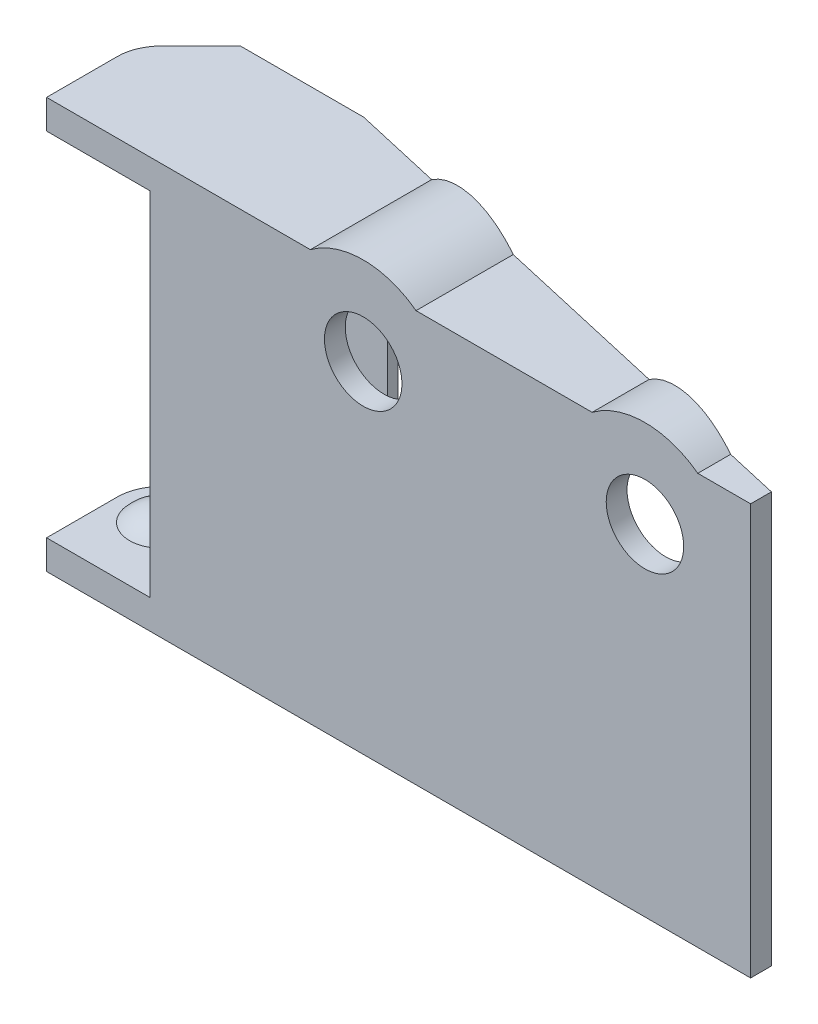
SolidWorks part; units mm, degrees
ref_plane "Front Plane" through (0, 0, 0) normal (0, 0, 1) x (1, 0, 0)
ref_plane "Top Plane" through (0, 0, 0) normal (0, 1, 0) x (1, 0, 0)
ref_plane "Right Plane" through (0, 0, 0) normal (1, 0, 0) x (0, 0, -1)
sketch "Sketch1" plane through (0, 0, 0) normal (0, 0, 1) x (1, 0, 0)
  line L0 (-6.35, 0) -> (6.35, 0)
  line L1 (6.35, 0) -> (6.35, -9.525)
  line L2 (6.35, -9.525) -> (-6.35, -9.525)
  line L3 (-6.35, -9.525) -> (-6.35, 0)
  point P3 (0, -9.525)
  point P6 (0, 0)
  dimension "D1" = 9.525
  dimension "D2" = 12.7
sketch "Sketch3" plane through (0, 0, 0) normal (0, 1, 0) x (1, 0, 0)
  line L0 (6.35, 0) -> (-6.35, 0) construction
  line L1 (-6.35, 0) -> (6.35, 0) construction
  circle A0 centre (-6.35, 3.175) radius 3.175
  circle A1 centre (6.35, 3.175) radius 3.175
  dimension "D1" = 6.35
sketch "Sketch6" plane through (0, 0, 0) normal (0, 1, 0) x (1, 0, 0)
  line L0 (-6.35, 0) -> (-8.1461, 0) construction
  line L1 (-8.1461, 0) -> (-9.0713, 1.5395) construction
  line L2 (3.1496, 3.175) -> (3.1496, 8.2738)
  line L3 (4.5243, 0) -> (3.6069, 1.5264) construction
  line L4 (6.35, 0) -> (-6.35, 0) construction
  line L5 (-6.35, 0) -> (4.5243, 0) construction
  line L6 (-8.1461, 0) -> (-6.9899, -1.9238) construction
  line L7 (-6.9899, -1.9238) -> (3.1496, -1.9238)
  line L8 (5.5675, -1.7359) -> (4.5243, 0) construction
  line L9 (3.1496, 3.175) -> (3.1496, -1.9238)
  line L10 (-8.5951, 5.4201) -> (-5.7413, 8.2738)
  line L11 (-5.7413, 8.2738) -> (3.1496, 8.2738)
  line L12 (-9.525, 3.175) -> (-9.525, -1.9238)
  line L13 (-9.525, -1.9238) -> (-6.9899, -1.9238)
  line L14 (-6.9587, -1.9238) -> (-5.7413, 8.2738) construction
  circle A0 centre (-6.35, 3.175) radius 3.175 construction
  circle A1 centre (6.35, 3.175) radius 3.175 construction
  arc A2 (-8.5951, 5.4201) -> (-9.525, 3.175) centre (-6.35, 3.175) ccw
  arc A4 (3.1496, 3.175) -> (3.6069, 1.5264) centre (6.35, 3.175) ccw construction
  point P21 (-6.35, 3.175)
  dimension "D2" = 0.0254
  dimension "D4" = 45
extrude "Boss-Extrude2" add sketch "Sketch6" along normal blind 2.1082
sketch "Sketch7" plane through (0, 0, 0) normal (0, -1, 0) x (1, 0, 0)
  line L0 (-9.525, 1.9238) -> (3.1496, 1.9238) construction
  line L1 (-2.0506, 1.9238) -> (-2.0506, 0.4238)
  line L6 (6.35, -8.2738) -> (-4.018, -8.2738)
  line L7 (3.1496, -8.2738) -> (-5.7413, -8.2738) construction
  line L8 (3.1496, -8.2738) -> (-5.7413, -8.2738) construction
  line L9 (6.35, 1.9238) -> (-2.0506, 1.9238)
  arc A1 (6.35, -8.2738) -> (6.35, 1.9238) centre (6.35, -3.175) ccw
  arc A2 (-9.525, -3.175) -> (-8.5951, -5.4201) centre (-6.35, -3.175) ccw construction
  arc A3 (-9.525, -3.175) -> (-8.5951, -5.4201) centre (-6.35, -3.175) ccw
  circle A4 centre (-6.35, -3.175) radius 5.0988 construction
  arc A5 (-4.018, -8.2738) -> (-2.0506, 0.4238) centre (-6.35, -3.175) ccw
  dimension "D2" = 0.508
  dimension "D1" = 1.5
extrude "Boss-Extrude3" add sketch "Sketch7" along normal blind 0.9
ref_plane "Plane1" through (0, 0, -3.175) normal (0, 0, 1) x (1, 0, 0)
sketch "Sketch10" plane through (0, 0, -3.175) normal (0, 0, 1) x (1, 0, 0)
  line L0 (-3.175, 0) -> (-9.525, 0) construction
  line L1 (-6.35, 0) -> (-6.35, -1.066)
  line L2 (-6.35, -1.066) -> (-6.35, 0)
  line L3 (-6.35, 0) -> (-4.064, 0)
  line L4 (-4.064, 0) -> (-3.0643, 1.1914) construction
  line L5 (-9.525, 0) -> (-2.0506, 0) construction
  arc A0 (-6.35, -1.066) -> (-4.064, 0) centre (-6.35, 1.9182) ccw
  dimension "D1" = 2.286
  dimension "D2" = 50
revolve "Revolve2" add sketch "Sketch10" angle 360 about L1
sketch "Sketch11" plane through (0, 0, -3.175) normal (0, 0, 1) x (1, 0, 0)
  line L1 (9.525, 0) -> (3.175, 0) construction
  line L2 (8.89, 0) -> (9.5454, 0.781) construction
  line L3 (6.35, -0.9) -> (9.2786, -0.9)
  line L4 (6.35, -0.9) -> (11.4488, -0.9) construction
  line L6 (6.35, -0.9) -> (6.35, -2.0836)
  arc A0 (3.81, 0) -> (8.89, 0) centre (6.35, 2.1313) ccw construction
  arc A3 (6.35, -2.0836) -> (9.2786, -0.9) centre (6.35, 2.1313) ccw
  dimension "D1" = 50
  dimension "D2" = 2.54
  dimension "D3" = 0.8992
sketch "Sketch13" plane through (0, 0, 0) normal (0, -1, 0) x (1, 0, 0)
  line L1 (6.35, 1.9238) -> (-2.0506, 1.9238) construction
  line L2 (-2.0506, 0.4238) -> (3.1496, 0.4238)
  line L3 (-2.0506, 0.4238) -> (-2.0506, 1.9238)
  line L4 (-2.0506, 1.9238) -> (3.1496, 1.9238)
  line L5 (3.1496, 0.4238) -> (3.1496, 1.9238)
  line L6 (-2.0506, 0.4238) -> (3.1496, 1.9238) construction
  line L8 (-2.0506, 1.9238) -> (3.1496, 0.4238) construction
  arc A0 (-4.018, -8.2738) -> (-2.0506, 0.4238) centre (-6.35, -3.175) ccw construction
  point P0 (0.5495, 1.1738)
extrude "Boss-Extrude4" add sketch "Sketch13" along normal blind 12.7
sketch "Sketch16" plane through (0, -0.9, 0) normal (0, -1, 0) x (1, 0, 0)
  line L1 (6.35, -8.2738) -> (-0.7432, -8.2738)
  line L2 (6.35, -8.2738) -> (6.35, -6.7738)
  line L3 (6.35, -6.7738) -> (-0.7432, -6.7738)
  line L4 (-0.7432, -8.2738) -> (-0.7432, -6.7738)
  line L5 (3.1496, 0.4238) -> (3.1496, 1.9238) construction
  line L6 (-0.7432, -3.175) -> (-0.7432, -6.7738) construction
  line L7 (-9.525, -3.175) -> (-0.7432, -3.175) construction
  arc A0 (-4.018, -8.2738) -> (-2.0506, 0.4238) centre (-6.35, -3.175) ccw construction
  arc A1 (-4.018, -8.2738) -> (-2.0506, 0.4238) centre (-6.35, -3.175) ccw construction
extrude "Boss-Extrude5" add sketch "Sketch16" along normal up to vertex (11.8 mm away) up to point (3.1496, -12.7, 0.4238)
mirror "Mirror1" about plane through (3.1496, -12.7, 1.9238) normal (0, 1, 0) of bodies 117 110 114
sketch "Sketch17" plane through (3.1496, 0, 0) normal (1, 0, 0) x (0, 0, -1)
  line L4 (-0.4238, -0.9) -> (-1.9238, -0.9)
  line L5 (-1.9238, -0.9) -> (-1.9238, -24.5)
  line L6 (-1.9238, -24.5) -> (-0.4238, -24.5)
  line L7 (-0.4238, -24.5) -> (-0.4238, -0.9)
  line L8 (-0.4238, -0.9) -> (-1.9238, -0.9)
  line L9 (-1.9238, -0.9) -> (-1.9238, -24.5)
  line L10 (-1.9238, -24.5) -> (-0.4238, -24.5)
  line L11 (-0.4238, -24.5) -> (-0.4238, -0.9)
  dimension "D1" = 0
extrude "Boss-Extrude6" add sketch "Sketch17" along normal blind 38.1
sketch "Sketch18" plane through (0, -27.5082, 0) normal (0, -1, 0) x (1, 0, 0)
  line L0 (3.1496, -8.2738) -> (41.2496, 0.4238)
  line L1 (41.2496, 0.4238) -> (41.2496, 1.9238)
  line L2 (41.2496, 1.9238) -> (3.1496, 1.9238)
  line L3 (3.1496, 1.9238) -> (3.1496, -8.2738)
extrude "Boss-Extrude7" add sketch "Sketch18" against normal up to surface (3.0082 mm away) up to face at (24.7402, -24.5, 1.2638)
sketch "Sketch19" plane through (0, 2.1082, 0) normal (0, 1, 0) x (1, 0, 0)
  line L0 (3.1496, 8.2738) -> (41.2496, -0.4238)
  line L1 (41.2496, -0.4238) -> (41.2496, -1.9238)
  line L2 (41.2496, -1.9238) -> (3.1496, -1.9238)
  line L3 (3.1496, -1.9238) -> (3.1496, 8.2738)
extrude "Boss-Extrude8" add sketch "Sketch19" against normal up to surface (3.0082 mm away) up to face at (24.7402, -0.9, 1.2638)
sketch "Sketch20" plane through (0, -27.5082, 0) normal (0, -1, 0) x (1, 0, 0)
  line L2 (10.0313, -6.7028) -> (3.1496, -8.2738)
  line L3 (3.1496, -8.2738) -> (6.35, -8.2738)
  line L4 (10.0313, -6.7028) -> (3.1496, -8.2738)
  line L5 (3.1496, -8.2738) -> (6.35, -8.2738)
  arc A1 (6.35, -8.2738) -> (10.0313, -6.7028) centre (6.35, -3.175) ccw
  arc A2 (6.35, -8.2738) -> (10.0313, -6.7028) centre (6.35, -3.175) ccw
  dimension "D1" = 0
extrude "Cut-Extrude1" cut sketch "Sketch20" against normal through all
sketch "Sketch21" plane through (0, 0, 0.4238) normal (0, 0, -1) x (-1, 0, 0)
  line L0 (-30.8356, -2.9718) -> (-16.1036, -2.9718) construction
  line L1 (-41.2496, 2.1082) -> (-3.1496, 2.1082) construction
  line L2 (-41.2496, -24.5) -> (-41.2496, -0.9) construction
  circle A0 centre (-33.6296, -2.9718) radius 2.794
  circle A1 centre (-13.3096, -2.9718) radius 2.794
  dimension "D2" = 5.588
  dimension "D1" = 14.732
  dimension "D3" = 5.08
  dimension "D4" = 7.62
extrude "Cut-Extrude2" cut sketch "Sketch21" against normal up to next
sketch "Sketch22" plane through (0, 0, 0.4238) normal (0, 0, -1) x (-1, 0, 0)
  circle A0 centre (-33.6296, -2.9718) radius 4.572
  circle A1 centre (-13.3096, -2.9718) radius 4.572
  dimension "D1" = 9.144
extrude "Cut-Extrude3" cut sketch "Sketch22" along normal through all
sketch "Sketch23" plane through (0, 0, 0.4238) normal (0, 0, -1) x (-1, 0, 0)
  line L0 (-41.2496, 2.1082) -> (-3.1496, 2.1082) construction
  line L1 (-41.2496, 2.1082) -> (-3.1496, 2.1082)
  circle A0 centre (-33.6296, -2.9718) radius 6.35
  circle A1 centre (-13.3096, -2.9718) radius 6.35
  dimension "D1" = 12.7
extrude "Boss-Extrude9" add sketch "Sketch23" along normal up to surface and the other way up to surface (1.5 mm away) contours L1 A0 | L1 A1
